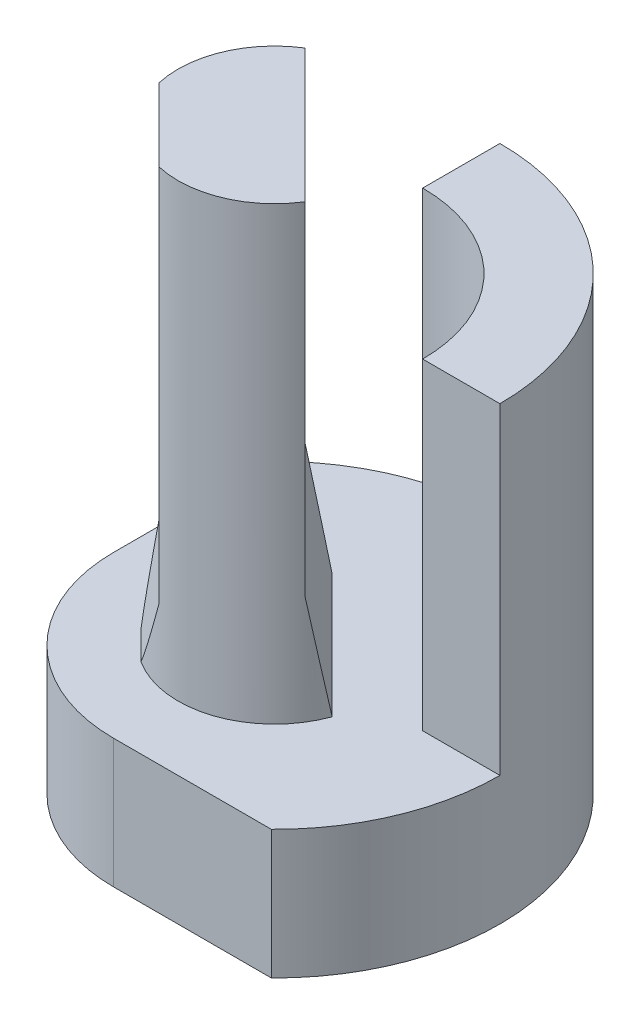
SolidWorks part; units mm, degrees
ref_plane "Front Plane" through (0, 0, 0) normal (0, 0, 1) x (1, 0, 0)
ref_plane "Top Plane" through (0, 0, 0) normal (0, 1, 0) x (1, 0, 0)
ref_plane "Right Plane" through (0, 0, 0) normal (1, 0, 0) x (0, 0, -1)
sketch "Sketch1" plane through (0, 0, 0) normal (0, 1, 0) x (1, 0, 0)
  circle A0 centre (0, 0) radius 3.5
  dimension "D1" = 7
extrude "Boss-Extrude1" add sketch "Sketch1" along normal blind 2
sketch "Sketch2" plane through (0, 2, 0) normal (0, 1, 0) x (1, 0, 0)
  circle A0 centre (0, 0) radius 1.5
  dimension "D1" = 3
extrude "Boss-Extrude2" add sketch "Sketch2" along normal blind 7
chamfer "Chamfer1" [suppressed] distance 0.3 angle 80
sketch "Sketch5" plane through (0, 2, 0) normal (0, 1, 0) x (1, 0, 0)
  line L0 (-2.2287, 2.6987) -> (2.6987, -2.2287)
  line L1 (-3.2032, 1.4105) -> (1.4105, -3.2032)
  circle A0 centre (0, 0) radius 3.5 construction
  arc A1 (-2.2287, 2.6987) -> (-3.2032, 1.4105) centre (0, 0) ccw
  arc A2 (1.4105, -3.2032) -> (2.6987, -2.2287) centre (0, 0) ccw
  dimension "D1" = 1.6
extrude "Cut-Extrude1" cut sketch "Sketch5" along normal blind 7 flip side to cut
sketch "Sketch4" plane through (0, 2, 0) normal (0, 1, 0) x (1, 0, 0)
  line L0 (0, 2.3) -> (0, 3.5)
  line L1 (2.3, 0) -> (3.5, 0)
  circle A0 centre (0, 0) radius 3.5 construction
  arc A1 (3.5, 0) -> (0, 3.5) centre (0, 0) ccw
  arc A2 (2.3, 0) -> (0, 2.3) centre (0, 0) ccw
  circle A4 centre (0, 0) radius 3.5 construction
  circle A5 centre (0, 0) radius 2.3 construction
  point P2 (2.5, 0)
  point P5 (3.3471, 1.0233)
  dimension "D1" = 1.2
extrude "Boss-Extrude4" add sketch "Sketch4" along normal blind 5
chamfer "Chamfer3" distance 0.3 angle 80 1 edges at (0.235, 2, -0.235)
chamfer "Chamfer4" distance 0.2 angle 80 1 edges at (-0.8964, 2, 0.8964)
sketch "Sketch6" plane through (0, 2, 0) normal (0, 1, 0) x (1, 0, 0)
  line L0 (-2.5, 0) -> (-2.5, 2.4495)
  line L1 (0, -2.5) -> (2.4495, -2.5)
  arc A0 (-2.5, 0) -> (0, -2.5) centre (0, 0) ccw
  arc A1 (0, 3.5) -> (3.5, 0) centre (0, 0) ccw construction
  arc A2 (-2.5, 2.4495) -> (2.4495, -2.5) centre (0, 0) ccw
  dimension "D1" = 5
extrude "Cut-Extrude2" cut sketch "Sketch6" against normal through all
